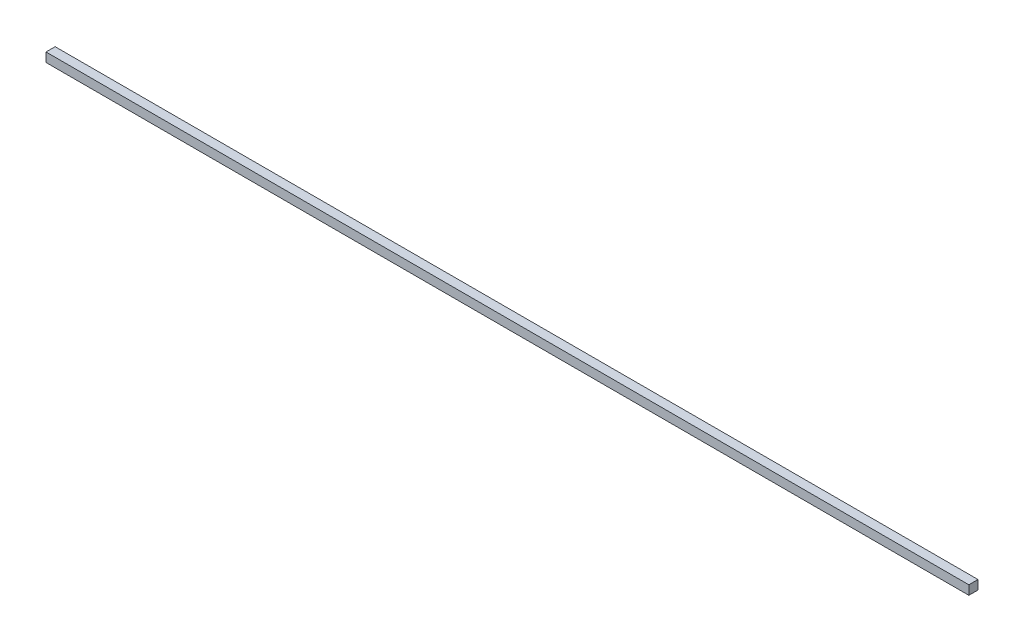
SolidWorks part; units mm, degrees
ref_plane "Front Plane" through (0, 0, 0) normal (0, 0, 1) x (1, 0, 0)
ref_plane "Top Plane" through (0, 0, 0) normal (0, 1, 0) x (1, 0, 0)
ref_plane "Right Plane" through (0, 0, 0) normal (1, 0, 0) x (0, 0, -1)
sketch "Sketch1" plane through (0, 0, 0) normal (0, 1, 0) x (1, 0, 0)
  line L0 (-505, 5) -> (505, -5) construction
  line L1 (-505, 5) -> (505, 5)
  line L2 (-505, 5) -> (-505, -5)
  line L3 (-505, -5) -> (505, -5)
  line L4 (505, 5) -> (505, -5)
  dimension "D1" = 1010
  dimension "D2" = 10
extrude "Boss-Extrude1" add sketch "Sketch1" along normal blind 10
